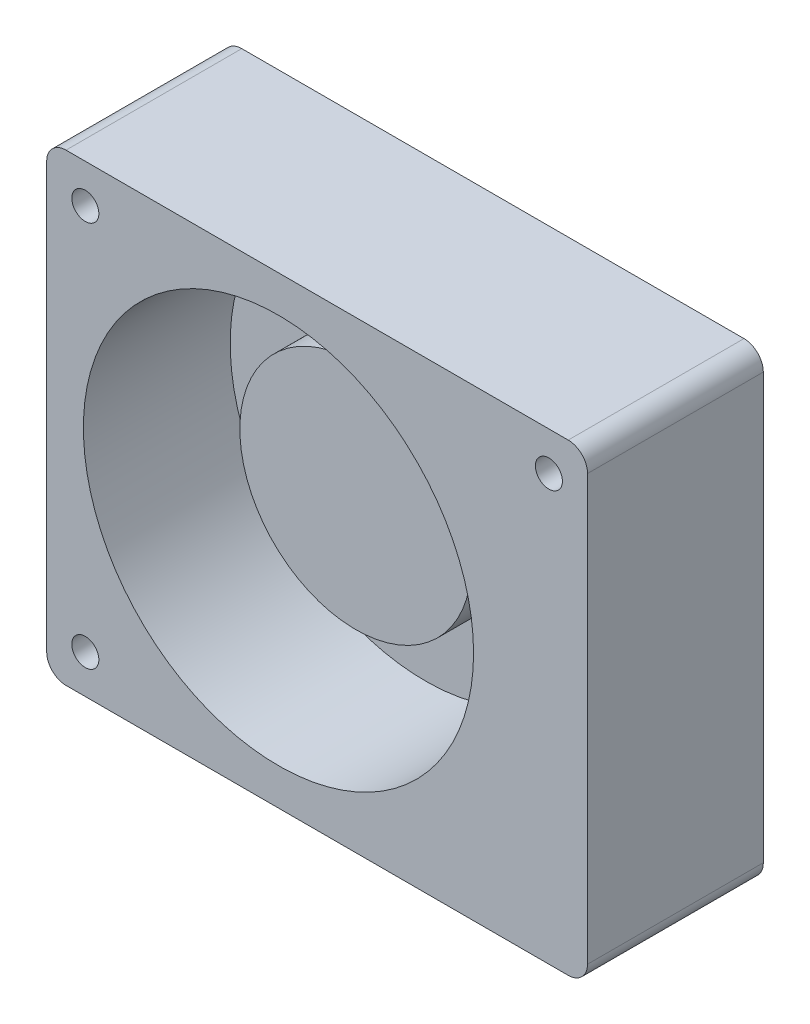
SolidWorks part; units mm, degrees
ref_plane "Front Plane" through (0, 0, 0) normal (0, 0, 1) x (1, 0, 0)
ref_plane "Top Plane" through (0, 0, 0) normal (0, 1, 0) x (1, 0, 0)
ref_plane "Right Plane" through (0, 0, 0) normal (1, 0, 0) x (0, 0, -1)
sketch "Sketch1" plane through (0, 0, 0) normal (0, 0, 1) x (1, 0, 0)
  line L0 (0, 5) -> (0, 115)
  line L1 (5, 120) -> (135, 120)
  line L2 (140, 115) -> (140, 5)
  line L3 (135, 0) -> (5, 0)
  arc A0 (135, 0) -> (140, 5) centre (135, 5) ccw
  arc A1 (0, 115) -> (5, 120) centre (5, 115) cw
  arc A2 (0, 5) -> (5, 0) centre (5, 5) ccw
  arc A3 (140, 115) -> (135, 120) centre (135, 115) ccw
  point P6 (140, 0)
  point P10 (0, 120)
  point P13 (0, 0)
  point P16 (140, 120)
  dimension "D3" = 5
  dimension "D1" = 140
  dimension "D2" = 120
extrude "Boss-Extrude1" add sketch "Sketch1" along normal blind 45.5
sketch "Sketch3" plane through (0, 0, 45.5) normal (0, 0, 1) x (1, 0, 0)
  line L0 (135, 120) -> (5, 120) construction
  line L1 (0, 115) -> (0, 5) construction
  line L3 (140, 5) -> (140, 115) construction
  line L4 (5, 0) -> (135, 0) construction
  circle A0 centre (10, 110) radius 3.5
  circle A1 centre (130, 110) radius 3.5
  circle A2 centre (10, 10) radius 3.5
  point P10 (0, 0)
  point P12 (130, 109.9074)
  dimension "D1" = 7
  dimension "D2" = 7
  dimension "D3" = 7
  dimension "D4" = 10
  dimension "D5" = 10
  dimension "D6" = 10
  dimension "D7" = 10
  dimension "D8" = 10
  dimension "D9" = 10
extrude "Cut-Extrude1" cut sketch "Sketch3" against normal through all
sketch "Sketch5" plane through (0, 0, 45.5) normal (0, 0, 1) x (1, 0, 0)
  line L0 (0, 60) -> (60, 60) construction
  line L1 (0, 115) -> (0, 5) construction
  circle A0 centre (60, 60) radius 30
  circle A1 centre (60, 60) radius 50.5
  dimension "D1" = 101
  dimension "D3" = 60
  dimension "D2" = 60
extrude "Cut-Extrude2" cut sketch "Sketch5" against normal blind 38
sketch "Sketch6" plane through (0, 0, 45.5) normal (0, 0, 1) x (1, 0, 0)
  circle A0 centre (60, 60) radius 30
extrude "Cut-Extrude3" cut sketch "Sketch6" against normal blind 20
